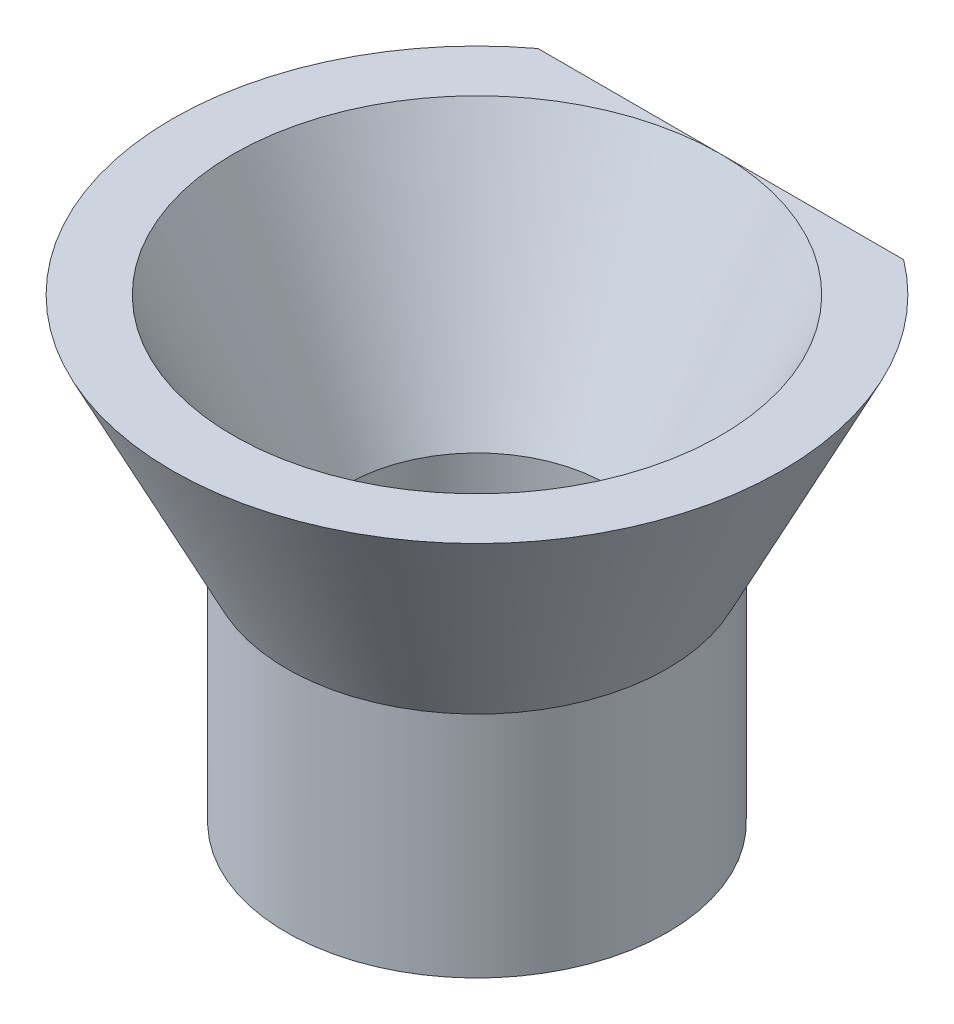
SolidWorks part; units mm, degrees
ref_plane "Alzado" through (0, 0, 0) normal (0, 0, 1) x (1, 0, 0)
ref_plane "Planta" through (0, 0, 0) normal (0, 1, 0) x (1, 0, 0)
ref_plane "Vista lateral" through (0, 0, 0) normal (1, 0, 0) x (0, 0, -1)
sketch "Croquis2" plane through (0, 0, 0) normal (0, 0, 1) x (1, 0, 0)
  line L0 (0, 0) -> (-4.25, 0) construction
  line L1 (-4.25, 0) -> (-8, 7.5)
  line L2 (-8, 7.5) -> (0, 7.5) construction
  line L3 (0, 7.5) -> (0, 0) construction
  line L4 (-8, 7.5) -> (-10, 7.5)
  line L5 (-10, 7.5) -> (-6.25, 0)
  line L6 (-6.25, 0) -> (-4.25, 0)
  dimension "D1" = 7.5
  dimension "D2" = 8
  dimension "D3" = 4.25
  dimension "D4" = 2
  dimension "D5" = 2
revolve "Revolución1" add sketch "Croquis2" angle 360 about L3
sketch "Croquis3" plane through (0, 0, 0) normal (0, -1, 0) x (1, 0, 0)
  circle A0 centre (0, 0) radius 4.25
  circle A1 centre (0, 0) radius 6.25
  dimension "D1" = 8.5
  dimension "D2" = 2
extrude "Saliente-Extruir1" add sketch "Croquis3" along normal blind 7.5
sketch "Croquis4" plane through (0, 7.5, 0) normal (0, 1, 0) x (1, 0, 0)
  line L0 (-7.8165, 8) -> (7.8165, 8)
  line L1 (7.8165, 8) -> (0, 11.4586)
  line L2 (0, 11.4586) -> (-7.8165, 8)
  point P3 (0, 8)
extrude "Cortar-Extruir1" cut sketch "Croquis4" against normal blind 10
